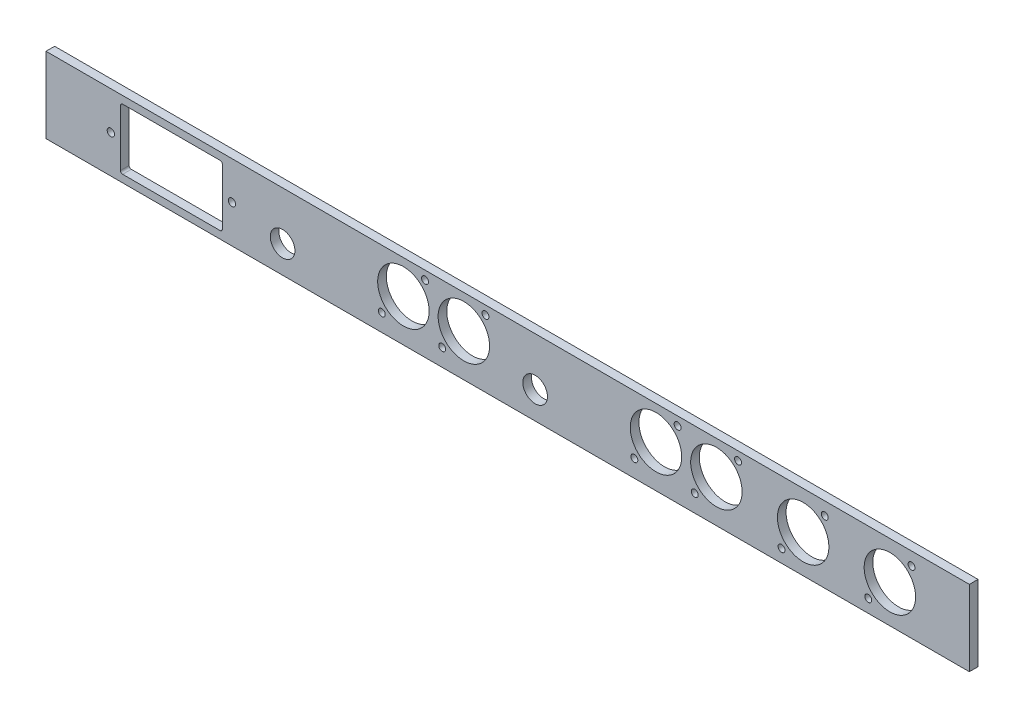
SolidWorks part; units mm, degrees
ref_plane "Front Plane" through (0, 0, 0) normal (0, 0, 1) x (1, 0, 0)
ref_plane "Top Plane" through (0, 0, 0) normal (0, 1, 0) x (1, 0, 0)
ref_plane "Right Plane" through (0, 0, 0) normal (1, 0, 0) x (0, 0, -1)
sketch "Sketch1" plane through (0, 0, 0) normal (0, 0, 1) x (1, 0, 0)
  line L0 (0, 17.5) -> (0, -17.5) construction
  line L1 (-213.5, -17.5) -> (213.5, -17.5)
  line L2 (-213.5, -17.5) -> (-213.5, 17.5)
  line L3 (-213.5, 17.5) -> (213.5, 17.5)
  line L4 (213.5, -17.5) -> (213.5, 17.5)
  line L5 (0, 0) -> (-213.5, 0) construction
  dimension "D1" = 427
  dimension "D2" = 35
extrude "Boss-Extrude1" add sketch "Sketch1" along normal blind 4
sketch "Sketch2" plane through (0, 0, 4) normal (0, 0, 1) x (1, 0, 0)
  line L0 (-116.7918, -2.28) -> (-116.7918, 4.0779) construction
  line L1 (-213.5, 17.5) -> (-213.5, -17.5) construction
  line L2 (-213.5, -17.5) -> (213.5, -17.5) construction
  line L3 (-20.2718, 13.9) -> (-20.2718, -9.9) construction
  line L4 (-48.2118, 13.5) -> (-48.2118, -10.66) construction
  line L6 (-48.2118, 13.5) -> (-38.2118, 13.5) construction
  line L7 (-3.0018, 2.6808) -> (-3.0018, -15.3691) construction
  line L8 (-116.7918, -2.28) -> (-116.7918, 4.0779) construction
  line L9 (-113.1918, 7.9605) -> (-94.9918, 7.9605) construction
  line L11 (0, 17.5) -> (0, -17.5) construction
  line L12 (213.5, 17.5) -> (-213.5, 17.5) construction
  line L15 (-179.05, -14.05) -> (-131.95, 14.05) construction
  line L17 (113.79, 17.5) -> (113.79, -17.2396) construction
  line L18 (-179.05, 14.05) -> (-131.95, -14.05) construction
  line L19 (-213.5, -17.5) -> (213.5, -17.5) construction
  line L20 (-85.2518, 7.9605) -> (-67.0518, 7.9605) construction
  line L21 (87.4177, 2) -> (87.4177, 6.5526) construction
  line L23 (-20.2718, 0) -> (-20.2718, 17.5) construction
  line L25 (-200.5, 17.5) -> (-200.5, -17.5) construction
  line L26 (-213.5, -17.5) -> (213.5, -17.5) construction
  line L27 (-213.5, 17.5) -> (-213.5, -17.5) construction
  line L28 (200.5, -17.5) -> (200.5, 17.5) construction
  line L29 (213.5, -17.5) -> (213.5, 17.5) construction
  line L30 (-213.5, 17.5) -> (213.5, 17.5) construction
  line L34 (-178.05, -14.05) -> (-132.95, -14.05)
  line L35 (-179.05, -13.05) -> (-179.05, 13.05)
  line L36 (-178.05, 14.05) -> (-132.95, 14.05)
  line L37 (-131.95, -13.05) -> (-131.95, 13.05)
  line L38 (0, 17.5) -> (113.79, 17.5) construction
  circle A0 centre (-20.2718, 2) radius 11.9
  circle A1 centre (-30.2718, -9.5) radius 1.6
  circle A2 centre (-10.2718, 13.5) radius 1.6
  circle A3 centre (-58.2118, -9.5) radius 1.6
  circle A4 centre (-48.2118, 2) radius 11.9
  circle A5 centre (-38.2118, 13.5) radius 1.6
  circle A6 centre (126.64, -11.5) radius 1.6
  circle A7 centre (146.64, 11.5) radius 1.6
  circle A8 centre (136.64, 0) radius 11.9
  circle A9 centre (166.76, -11.5) radius 1.6
  circle A10 centre (186.76, 11.5) radius 1.6
  circle A11 centre (176.76, 0) radius 11.9
  circle A13 centre (-104.0918, -4.865) radius 5.7
  circle A15 centre (86.52, -9.5) radius 1.6
  circle A16 centre (106.52, 13.5) radius 1.6
  circle A17 centre (68.58, 2) radius 11.9
  circle A18 centre (96.52, 2) radius 11.9
  circle A19 centre (12.7, -4.865) radius 5.7
  circle A20 centre (78.58, 13.5) radius 1.6
  circle A21 centre (58.58, -9.5) radius 1.6
  circle A22 centre (-127.5, 0) radius 1.7
  arc A23 (-178.05, -14.05) -> (-179.05, -13.05) centre (-178.05, -13.05) cw
  arc A24 (-131.95, 13.05) -> (-132.95, 14.05) centre (-132.95, 13.05) ccw
  arc A25 (-131.95, -13.05) -> (-132.95, -14.05) centre (-132.95, -13.05) cw
  arc A26 (-179.05, 13.05) -> (-178.05, 14.05) centre (-178.05, 13.05) cw
  circle A27 centre (-183.5, 0) radius 1.7
  point P14 (102.4845, 2)
  point P27 (-60.9232, 2)
  point P32 (-8.3718, 2)
  point P42 (-109.9732, -5.125)
  point P48 (7.2368, 2)
  point P49 (7.2352, -5.0363)
  point P52 (7.2368, 2)
  point P54 (142.6045, 0)
  point P77 (50.6845, 2)
  point P104 (-179.05, 0)
  point P123 (182.7245, 0)
  dimension "D2" = 3.2
  dimension "D6" = 11.4
  dimension "D9" = 13
  dimension "D22" = 4.45
  dimension "D12" = 4.45
  dimension "D27" = 1
  dimension "D28" = 11.4
  dimension "D19" = 47.1
  dimension "D30" = 27.94
  dimension "D32" = 10
  dimension "D33" = 10
  dimension "D34" = 23.8
  dimension "D35" = 10
  dimension "D36" = 20
  dimension "D37" = 23
  dimension "D38" = 23
  dimension "D39" = 23.8
  dimension "D40" = 23.8
  dimension "D41" = 23.8
  dimension "D42" = 3.0018
  dimension "D14" = 20
  dimension "D15" = 23
  dimension "D16" = 10
  dimension "D18" = 12.7
  dimension "D45" = 11.5
  dimension "D47" = 11.5
  dimension "D48" = 11.5
  dimension "D49" = 10
  dimension "D50" = 11.5
  dimension "D51" = 9.1
  dimension "D13" = 10
  dimension "D20" = 17.27
  dimension "D5" = 23
  dimension "D8" = 27.94
  dimension "D10" = 13
  dimension "D17" = 12.7
  dimension "D21" = 19.5
  dimension "D24" = 34.45
  dimension "D25" = 28.1
  dimension "D46" = 11.5
  dimension "D52" = 17.27
  dimension "D53" = 9.1
extrude "Cut-Extrude1" cut sketch "Sketch2" against normal blind 4
